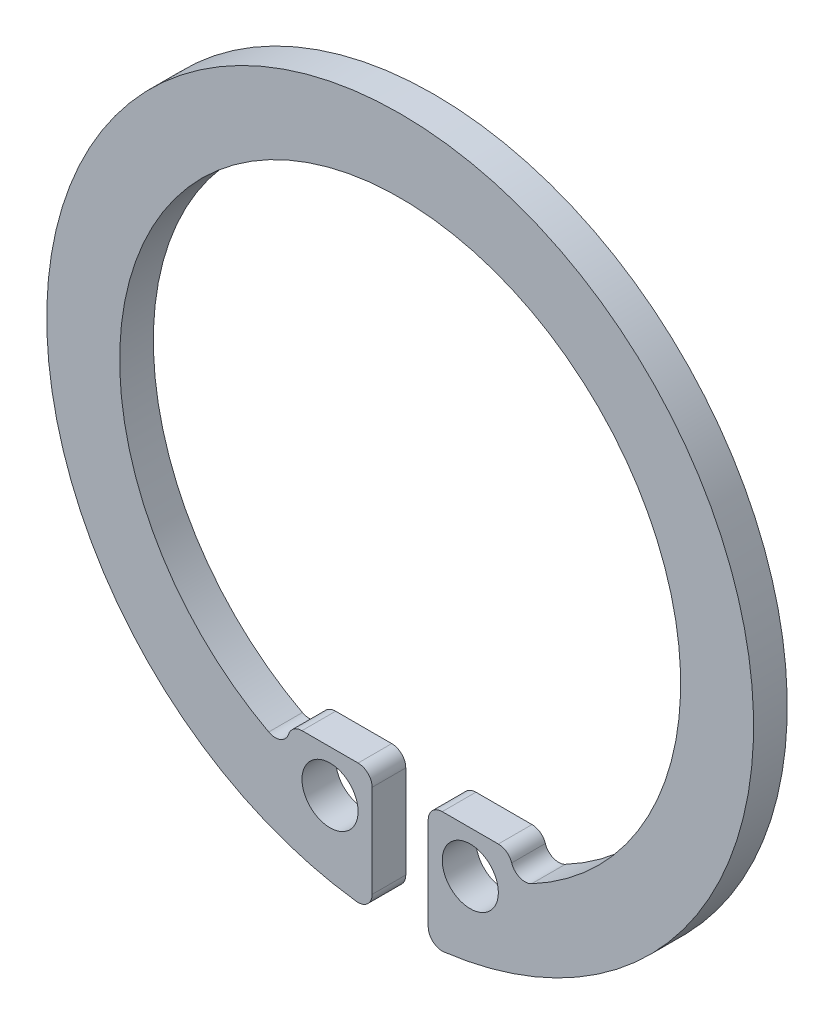
SolidWorks part; units mm, degrees
material "1.4122 (X39CrMo17-1)"
ref_plane "Płaszczyzna XY" through (0, 0, 0) normal (0, 0, 1) x (1, 0, 0)
ref_plane "Płaszczyzna XZ" through (0, 0, 0) normal (0, 1, 0) x (1, 0, 0)
ref_plane "Płaszczyzna YZ" through (0, 0, 0) normal (1, 0, 0) x (0, 0, -1)
sketch "Szkic1" plane through (0, 0, 0) normal (0, 0, 1) x (1, 0, 0)
  line L0 (2.5, -4.0721) -> (2.5, -9.2878) construction
  line L1 (-1, -12.5603) -> (-1, -8.2)
  line L2 (0, 10.8988) -> (0, -12.1935) construction
  line L3 (1, -12.5603) -> (1, -8.2)
  line L4 (1, -8.2) -> (4, -8.2)
  line L5 (4, -9.1652) -> (4, -8.2)
  line L6 (-4, -9.1652) -> (-4, -8.2)
  line L7 (-1, -8.2) -> (-4, -8.2)
  arc A0 (1, -12.5603) -> (-1, -12.5603) centre (0, 0) ccw
  arc A1 (4, -9.1652) -> (-4, -9.1652) centre (0, 0) ccw
  circle A2 centre (2.5, -9.7) radius 1
  circle A3 centre (-2.5, -9.7) radius 1
  point P10 (0, -12.6)
  point P14 (2.5, -8.2)
  dimension "D1" = 25.2
  dimension "D2" = 2.6
  dimension "D3" = 2
  dimension "D4" = 4.4
  dimension "D5" = 1
  dimension "D6" = 3
  dimension "D7" = 1.5
extrude "Dodanie-wyciągnięcie1" add sketch "Szkic1" along normal blind 1.2
fillet "Zaokrąglenie2" radius 0.5 1 edges at (1, -12.5603, 0.6)
fillet "Zaokrąglenie3" radius 0.5 1 edges at (-1, -12.5603, 0.6)
fillet "Zaokrąglenie4" radius 0.5 1 edges at (1, -8.2, 0.6)
fillet "Zaokrąglenie5" radius 0.5 1 edges at (4, -8.2, 0.6)
fillet "Zaokrąglenie6" radius 0.5 1 edges at (4, -9.1652, 0.6)
fillet "Zaokrąglenie7" radius 0.5 1 edges at (-4, -8.2, 0.6)
fillet "Zaokrąglenie8" radius 0.5 1 edges at (-1, -8.2, 0.6)
fillet "Zaokrąglenie9" radius 0.5 1 edges at (-4, -9.1652, 0.6)
